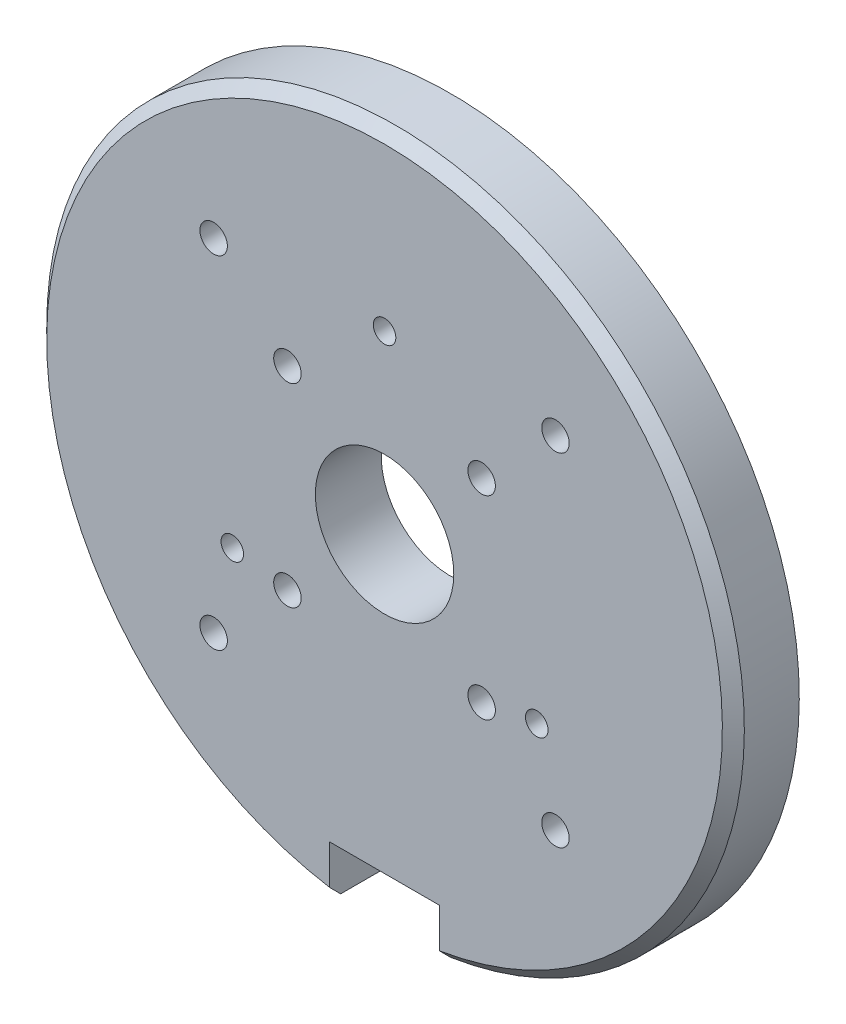
SolidWorks part; units mm, degrees
material "Сплав 2024"
ref_plane "Спереди" through (0, 0, 0) normal (0, 0, 1) x (1, 0, 0)
ref_plane "Сверху" through (0, 0, 0) normal (0, 1, 0) x (1, 0, 0)
ref_plane "Справа" through (0, 0, 0) normal (1, 0, 0) x (0, 0, -1)
sketch "Эскиз1" plane through (0, 0, 0) normal (0, 0, 1) x (1, 0, 0)
  circle A0 centre (0, 0) radius 31.75
  dimension "D1" = 63.5
extrude "Бобышка-Вытянуть1" add sketch "Эскиз1" along normal blind 6
sketch "Эскиз2" plane through (0, 0, 6) normal (0, 0, 1) x (1, 0, 0)
  line L0 (0, 16) -> (0, 0) construction
  line L1 (0, 0) -> (13.8564, -8) construction
  line L2 (0, 0) -> (-13.8564, -8) construction
  line L3 (0, 0) -> (0, -31.75) construction
  line L5 (-5, -26.75) -> (5, -26.75)
  line L6 (-5, -26.75) -> (-5, -36.75)
  line L7 (-5, -36.75) -> (5, -36.75)
  line L8 (5, -26.75) -> (5, -36.75)
  line L9 (-5, -26.75) -> (5, -36.75) construction
  line L10 (-5, -36.75) -> (5, -26.75) construction
  circle A0 centre (0, 0) radius 16 construction
  circle A1 centre (0, 0) radius 31.75 construction
  dimension "D1" = 32
  dimension "D2" = 120
  dimension "D3" = 120
  dimension "D4" = 10
  dimension "D5" = 10
extrude "Вырез-Вытянуть1" cut sketch "Эскиз2" against normal through all
hole_wizard "Отверстие обработанное метчиком M2.5x0.451" positions "Эскиз4" profile "Эскиз3" tap size "M2.5x0.45" standard "Ansi Metric" end condition through all
sketch "Эскиз4" plane through (0, 0, 6) normal (0, 0, 1) x (1, 0, 0)
  point P0 (0, 16)
  point P3 (13.8564, -8)
  point P6 (-13.8564, -8)
sketch "Эскиз3" plane through (0, 16, 6) normal (1, 0, 0) x (0, -1, 0)
  line L0 (0, 0) -> (0, 6)
  line L1 (0, 6) -> (1.025, 6)
  line L2 (1.025, 6) -> (1.025, 0)
  line L5 (1.025, 0) -> (0, 0)
  line L11 (0, -6.35) -> (0, 107.95) construction
  dimension "Диаметр проходного сверла" = 2.05
  dimension "Глубина проходного сверла" = 6
cosmetic thread "Отверстие резьбы1" parameters "D2"=2.5
cosmetic thread "Отверстие резьбы2" parameters "D2"=2.5
cosmetic thread "Отверстие резьбы3" parameters "D2"=2.5
sketch "Эскиз5" plane through (0, 0, 6) normal (0, 0, 1) x (1, 0, 0)
  line L0 (-15.5563, 15.5563) -> (15.5563, -15.5563) construction
  line L1 (15.5563, 15.5563) -> (-15.5563, -15.5563) construction
  line L2 (0, 16) -> (0, 0) construction
  circle A0 centre (0, 0) radius 12.5 construction
  circle A1 centre (0, 0) radius 22 construction
  dimension "D1" = 25
  dimension "D4" = 44
  dimension "D2" = 45
  dimension "D3" = 90
hole_wizard "Отверстие обработанное метчиком M3x0.51" positions "Эскиз7" profile "Эскиз6" tap size "M3x0.5" standard "Ansi Metric" end condition through all
sketch "Эскиз7" plane through (0, 0, 6) normal (0, 0, 1) x (1, 0, 0)
  line L0 (15.5563, 15.5563) -> (-15.5563, -15.5563) construction
  line L1 (-15.5563, 15.5563) -> (15.5563, -15.5563) construction
  circle A0 centre (0, 0) radius 12.5 construction
  point P0 (-15.5563, 15.5563)
  point P3 (-15.5563, -15.5563)
  point P6 (15.5563, -15.5563)
  point P9 (15.5563, 15.5563)
  point P12 (8.8388, 8.8388)
  point P18 (-8.8388, 8.8388)
  point P22 (-8.8388, -8.8388)
  point P24 (8.8388, -8.8388)
sketch "Эскиз6" plane through (-15.5563, 15.5563, 6) normal (1, 0, 0) x (0, -1, 0)
  line L0 (0, 0) -> (0, 6)
  line L1 (0, 6) -> (1.25, 6)
  line L2 (1.25, 6) -> (1.25, 0)
  line L5 (1.25, 0) -> (0, 0)
  line L11 (0, -6.35) -> (0, 107.95) construction
  dimension "Диаметр проходного сверла" = 2.5
  dimension "Глубина проходного сверла" = 6
cosmetic thread "Отверстие резьбы4" parameters "D2"=3
cosmetic thread "Отверстие резьбы5" parameters "D2"=3
cosmetic thread "Отверстие резьбы6" parameters "D2"=3
cosmetic thread "Отверстие резьбы7" parameters "D2"=3
cosmetic thread "Отверстие резьбы8" parameters "D2"=3
cosmetic thread "Отверстие резьбы9" parameters "D2"=3
cosmetic thread "Отверстие резьбы10" parameters "D2"=3
cosmetic thread "Отверстие резьбы11" parameters "D2"=3
sketch "Эскиз8" plane through (0, 0, 6) normal (0, 0, 1) x (1, 0, 0)
  circle A0 centre (0, 0) radius 6.3
  dimension "D1" = 12.6
extrude "Вырез-Вытянуть2" cut sketch "Эскиз8" against normal through all
chamfer "Фаска1" distance 1 angle 45 1 edges at (0, 31.75, 6)
